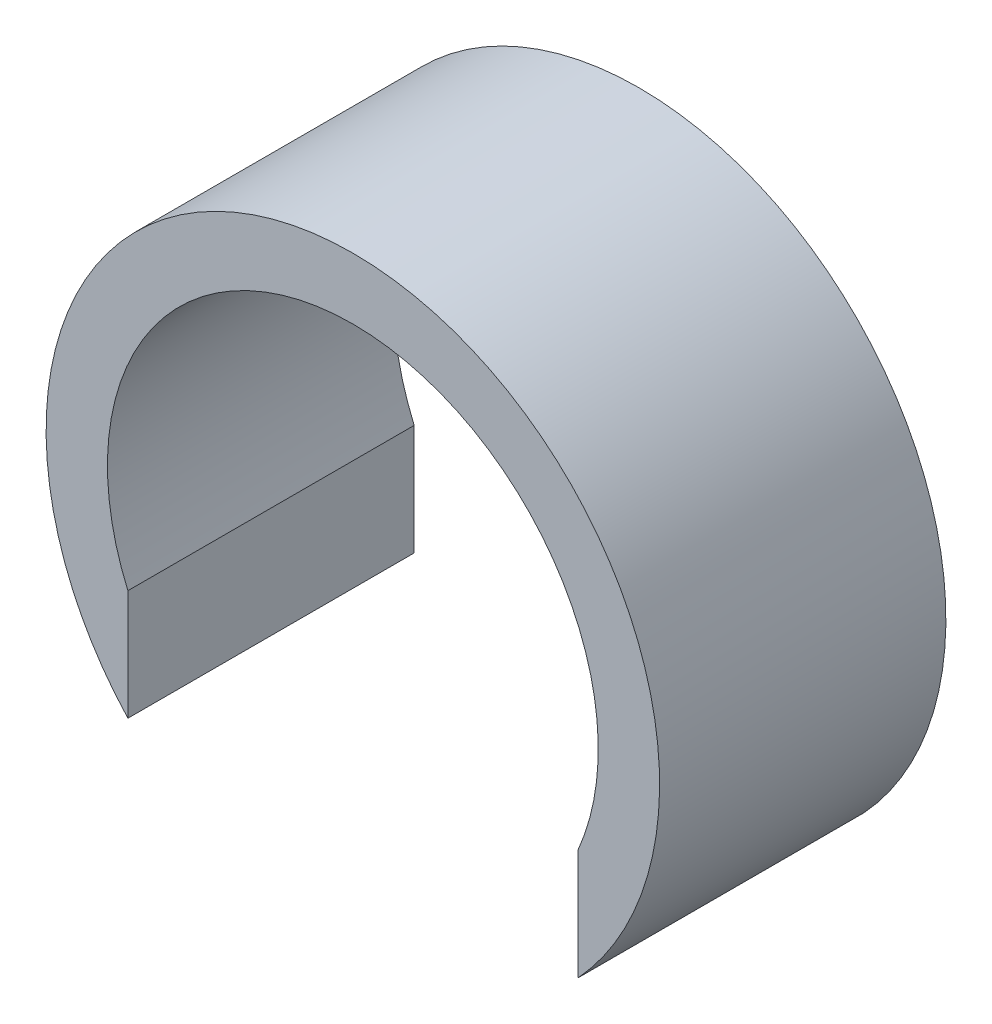
SolidWorks part; units mm, degrees
ref_plane "正面" through (0, 0, 0) normal (0, 0, 1) x (1, 0, 0)
ref_plane "平面" through (0, 0, 0) normal (0, 1, 0) x (1, 0, 0)
ref_plane "右側面" through (0, 0, 0) normal (1, 0, 0) x (0, 0, -1)
sketch "ｽｹｯﾁ1" plane through (0, 0, 0) normal (0, 0, 1) x (1, 0, 0)
  line L3 (5.5, -5.099) -> (5.5, -2.3979)
  line L5 (-1.5, -10.7982) -> (1.5, -4.2018) construction
  line L6 (-1.5, -4.2018) -> (1.5, -10.7982) construction
  line L8 (-5.5, -5.099) -> (-5.5, -2.3979)
  line L9 (5.5, -19.9963) -> (-5.5, 0) construction
  line L10 (5.5, 0) -> (-5.5, -19.9963) construction
  arc A0 (5.5, -2.3979) -> (-5.5, -2.3979) centre (0, 0) ccw
  arc A1 (5.5, -5.099) -> (-5.5, -5.099) centre (0, 0) ccw
  point P1 (0, -9.9982)
  point P4 (0, -7.5)
  dimension "D1" = 12
  dimension "D2" = 15
  dimension "D3" = 3
  dimension "D4" = 11
extrude "ﾎﾞｽ - 押し出し1" add sketch "ｽｹｯﾁ1" along normal blind 7
